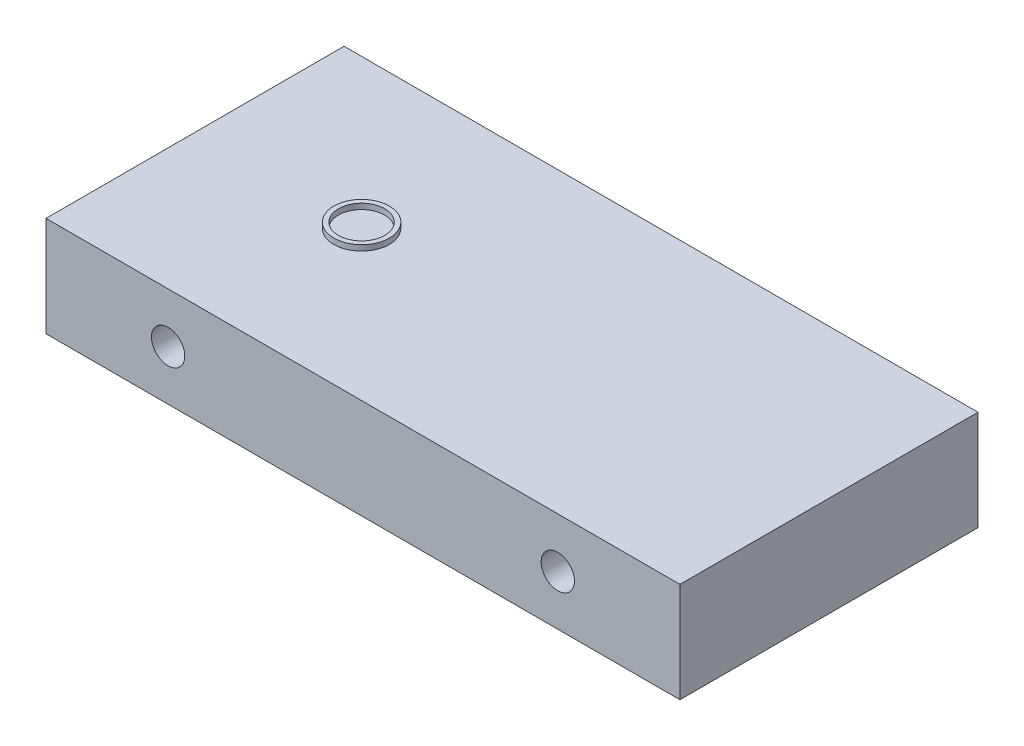
SolidWorks part; units mm, degrees
ref_plane "Front Plane" through (0, 0, 0) normal (0, 0, 1) x (1, 0, 0)
ref_plane "Top Plane" through (0, 0, 0) normal (0, 1, 0) x (1, 0, 0)
ref_plane "Right Plane" through (0, 0, 0) normal (1, 0, 0) x (0, 0, -1)
sketch "Sketch1" plane through (0, 0, 0) normal (0, 1, 0) x (1, 0, 0)
  line L1 (-171.2717, -80.5339) -> (171.2717, -80.5339)
  line L2 (-171.2717, -80.5339) -> (-171.2717, 80.5339)
  line L3 (-171.2717, 80.5339) -> (171.2717, 80.5339)
  line L4 (171.2717, -80.5339) -> (171.2717, 80.5339)
  line L5 (-171.2717, -80.5339) -> (171.2717, 80.5339) construction
  line L6 (-171.2717, 80.5339) -> (171.2717, -80.5339) construction
  point P0 (0, 0)
  dimension "D1" = 161.0678
  dimension "D2" = 342.5435
extrude "Boss-Extrude1" add sketch "Sketch1" along normal blind 54
sketch "Sketch3" plane through (0, 0, -80.5339) normal (0, 0, -1) x (-1, 0, 0)
  line L0 (-171.2717, 27) -> (-105.2849, 27) construction
  line L1 (-171.2717, 54) -> (-171.2717, 0) construction
  line L2 (171.2717, 27) -> (105.2849, 27) construction
  line L3 (171.2717, 54) -> (171.2717, 0) construction
  circle A0 centre (-105.2849, 27) radius 9
  circle A1 centre (105.2849, 27) radius 9
  dimension "D3" = 18
  dimension "D4" = 18
  dimension "D1" = 65.9868
  dimension "D2" = 65.9868
extrude "Cut-Extrude1" cut sketch "Sketch3" against normal blind 340.02
sketch "Sketch4" plane through (0, 54, 0) normal (0, 1, 0) x (1, 0, 0)
  line L0 (-171.2717, 0) -> (-81.2717, 0) construction
  line L1 (-171.2717, 80.5339) -> (-171.2717, -80.5339) construction
  circle A0 centre (-81.2717, 0) radius 12.5
  circle A1 centre (-81.2717, 0) radius 15
  dimension "D2" = 30
  dimension "D3" = 25
  dimension "D1" = 90
extrude "Boss-Extrude2" add sketch "Sketch4" along normal blind 3
